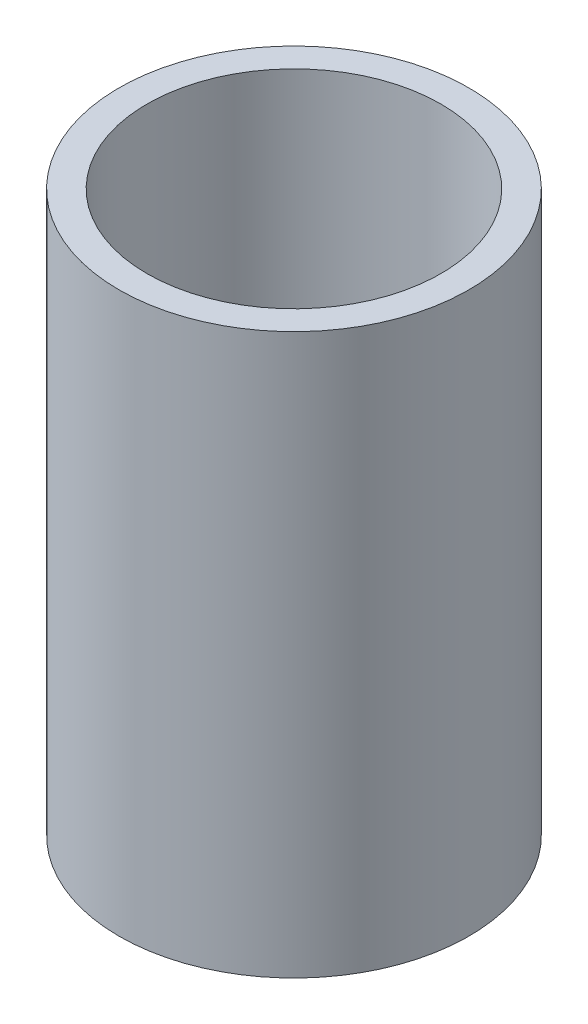
SolidWorks part; units mm, degrees
ref_plane "前视基准面" through (0, 0, 0) normal (0, 0, 1) x (1, 0, 0)
ref_plane "上视基准面" through (0, 0, 0) normal (0, 1, 0) x (1, 0, 0)
ref_plane "右视基准面" through (0, 0, 0) normal (1, 0, 0) x (0, 0, -1)
other "Configuration Table"
sketch "草图1" plane through (0, 0, 0) normal (0, 1, 0) x (1, 0, 0)
  circle A0 centre (0, 0) radius 10.5
  circle A1 centre (0, 0) radius 12.5
  dimension "D1" = 25
  dimension "D2" = 21
extrude "凸台-拉伸1" add sketch "草图1" along normal blind 40
